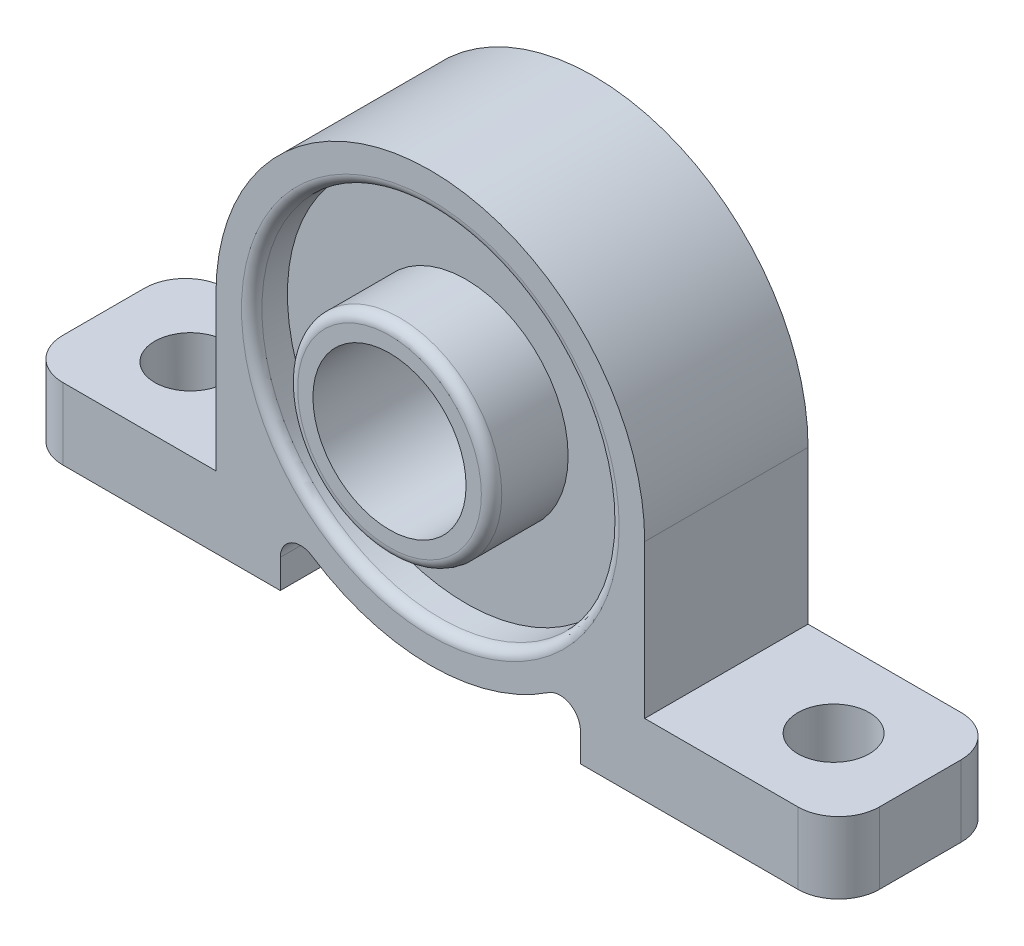
SolidWorks part; units mm, degrees
ref_plane "前视基准面" through (0, 0, 0) normal (0, 0, 1) x (1, 0, 0)
ref_plane "上视基准面" through (0, 0, 0) normal (0, 1, 0) x (1, 0, 0)
ref_plane "右视基准面" through (0, 0, 0) normal (1, 0, 0) x (0, 0, -1)
sketch "草图1" plane through (0, 0, 0) normal (0, 0, 1) x (1, 0, 0)
  line L0 (0, 22.8127) -> (0, -35.7252) construction
  line L1 (-40, 0) -> (-21, 0)
  line L2 (-40, 0) -> (-40, -7)
  line L3 (-40, -7) -> (-14.6969, -7)
  line L4 (40, 0) -> (40, -7)
  line L5 (-43.1281, 15) -> (45.7166, 15) construction
  line L6 (-21, 15) -> (-21, 0)
  line L7 (-14.6969, 0) -> (-14.6969, -7)
  line L8 (14.6969, 0) -> (14.6969, -7)
  line L9 (21, 15) -> (21, 0)
  line L10 (14.6969, -7) -> (40, -7)
  line L11 (21, 0) -> (40, 0)
  arc A0 (21, 15) -> (-21, 15) centre (0, 15) ccw
  circle A1 centre (0, 15) radius 7.5
  arc A2 (-14.6969, 0) -> (14.6969, 0) centre (0, 15) ccw
  point P14 (0, 0)
  point P21 (0, 0)
  point P22 (0, 0)
  point P23 (0, 0)
  point P24 (0, 0)
  dimension "D4" = 42
  dimension "D5" = 15
  dimension "D1" = 80
  dimension "D2" = 7
  dimension "D3" = 22
extrude "凸台-拉伸1" add sketch "草图1" along normal blind 16
sketch "草图2" plane through (0, 0, 16) normal (0, 0, 1) x (1, 0, 0)
  circle A0 centre (0, 15) radius 10
  circle A1 centre (0, 15) radius 7.5
  dimension "D1" = 20
extrude "凸台-拉伸2" add sketch "草图2" along normal blind 4
sketch "草图3" plane through (0, 0, 16) normal (0, 0, 1) x (1, 0, 0)
  circle A0 centre (0, 15) radius 10
  circle A1 centre (0, 15) radius 17.5
  dimension "D1" = 35
extrude "切除-拉伸1" cut sketch "草图3" against normal blind 3.5
sketch "草图4" plane through (0, 0, 0) normal (0, 0, -1) x (-1, 0, 0)
  circle A0 centre (0, 15) radius 17
  dimension "D1" = 34
extrude "切除-拉伸2" cut sketch "草图4" against normal blind 3.5
fillet "圆角1" radius 4 4 edges at (-40, -3.5, 16) (-40, -3.5, 0) (40, -3.5, 16) (40, -3.5, 0)
fillet "圆角2" radius 2 2 edges at (-14.6969, 0, 8) (14.6969, 0, 8)
fillet "圆角3" radius 1 4 edges at (-7.5, 15, 3.5) (-17, 15, 0) (17.5, 15, 16) (10, 15, 20)
sketch "草图5" plane through (0, 0, 0) normal (0, 1, 0) x (1, 0, 0)
  line L0 (-52.0856, -8) -> (55.9591, -8) construction
  line L1 (36, 0) -> (21, 0) construction
  line L2 (36, -16) -> (21, -16) construction
  line L3 (0, 19.5518) -> (0, -35.9952) construction
  circle A0 centre (-31.5, -8) radius 3.5
  circle A1 centre (31.5, -8) radius 3.5
  dimension "D1" = 63
  dimension "D2" = 7
extrude "切除-拉伸3" cut sketch "草图5" against normal through all and the other way through all contours A0
